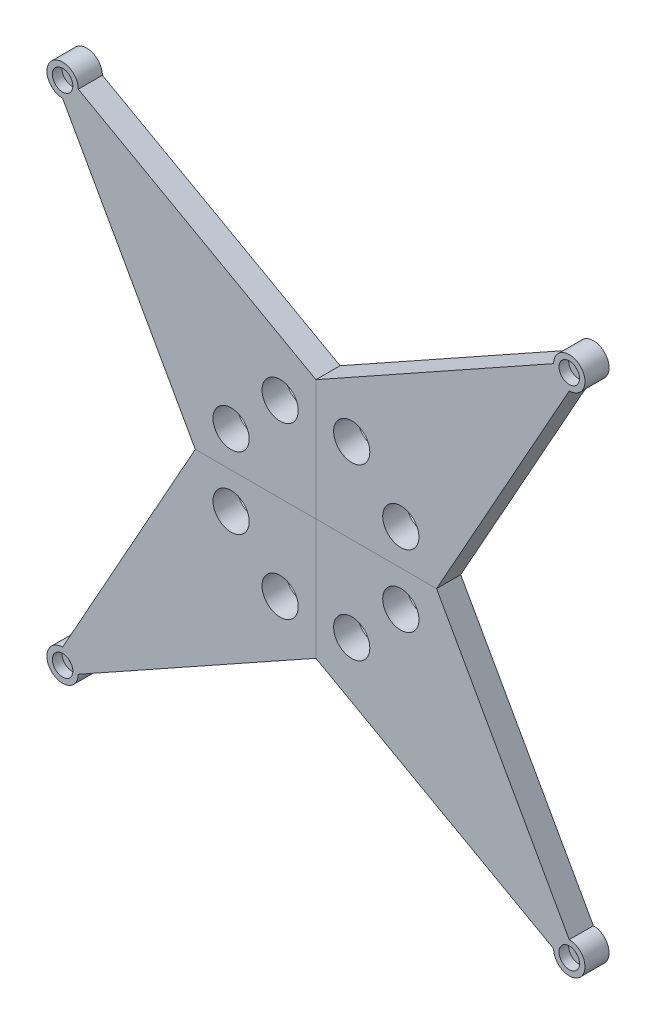
SolidWorks part; units mm, degrees
ref_plane "Plano frontal" through (0, 0, 0) normal (0, 0, 1) x (1, 0, 0)
ref_plane "Plano superior" through (0, 0, 0) normal (0, 1, 0) x (1, 0, 0)
ref_plane "Plano direito" through (0, 0, 0) normal (1, 0, 0) x (0, 0, -1)
sketch "Esboço3" plane through (0, 0, 0) normal (0, 0, 1) x (1, 0, 0)
  line L0 (-62.966, 0) -> (106.6858, 0) construction
  line L1 (0, 69.7378) -> (0, -73.302) construction
  line L2 (0, 50) -> (98.5, 105)
  line L3 (0, 0) -> (50, 0)
  line L4 (0, 0) -> (0, 50)
  line L7 (50, 0) -> (105, 98.5)
  arc A0 (105, 98.5) -> (98.5, 105) centre (105, 105) ccw
  dimension "D4" = 105
  dimension "D5" = 13
  dimension "D3" = 105
extrude "Ressalto-extrusão2" add sketch "Esboço3" along normal mid plane 10
sketch "Esboço4" plane through (0, 0, 5) normal (0, 0, 1) x (1, 0, 0)
  circle A0 centre (105, 105) radius 4.25
  arc A1 (105, 98.5) -> (98.5, 105) centre (105, 105) ccw construction
  dimension "D1" = 8.5
extrude "Corte-extrusão1" cut sketch "Esboço4" against normal blind 4 contours A0
sketch "Esboço5" plane through (0, 0, 1) normal (0, 0, 1) x (1, 0, 0)
  circle A0 centre (105, 105) radius 1.5
  circle A1 centre (105, 105) radius 4.25 construction
extrude "Corte-extrusão2" cut sketch "Esboço5" against normal through all
sketch "Esboço6" plane through (0, 0, 5) normal (0, 0, 1) x (1, 0, 0)
  line L0 (-26.6702, 0) -> (72.5742, 0) construction
  line L1 (0, 62.2144) -> (0, -11.4301) construction
  line L2 (0, 50) -> (63.2897, 50) construction
  line L3 (50, 0) -> (50, 50) construction
  line L4 (0, 50) -> (14.8256, 35.1744) construction
  line L5 (14.8256, 35.1744) -> (35.1744, 14.8256) construction
  line L6 (35.1744, 14.8256) -> (50, 0) construction
  line L7 (0, 0) -> (50, 50) construction
  circle A0 centre (14.8256, 35.1744) radius 7.5
  circle A1 centre (35.1744, 14.8256) radius 7.5
  point P16 (0, 0)
  dimension "D1" = 15
  dimension "D2" = 15
extrude "Corte-extrusão3" cut sketch "Esboço6" against normal through all
mirror "Espelhar1" about plane through (0, 0, 5) normal (0, 1, 0) of bodies 105
mirror "Espelhar2" about plane through (0, 0, 5) normal (1, 0, 0) of bodies 106 105
